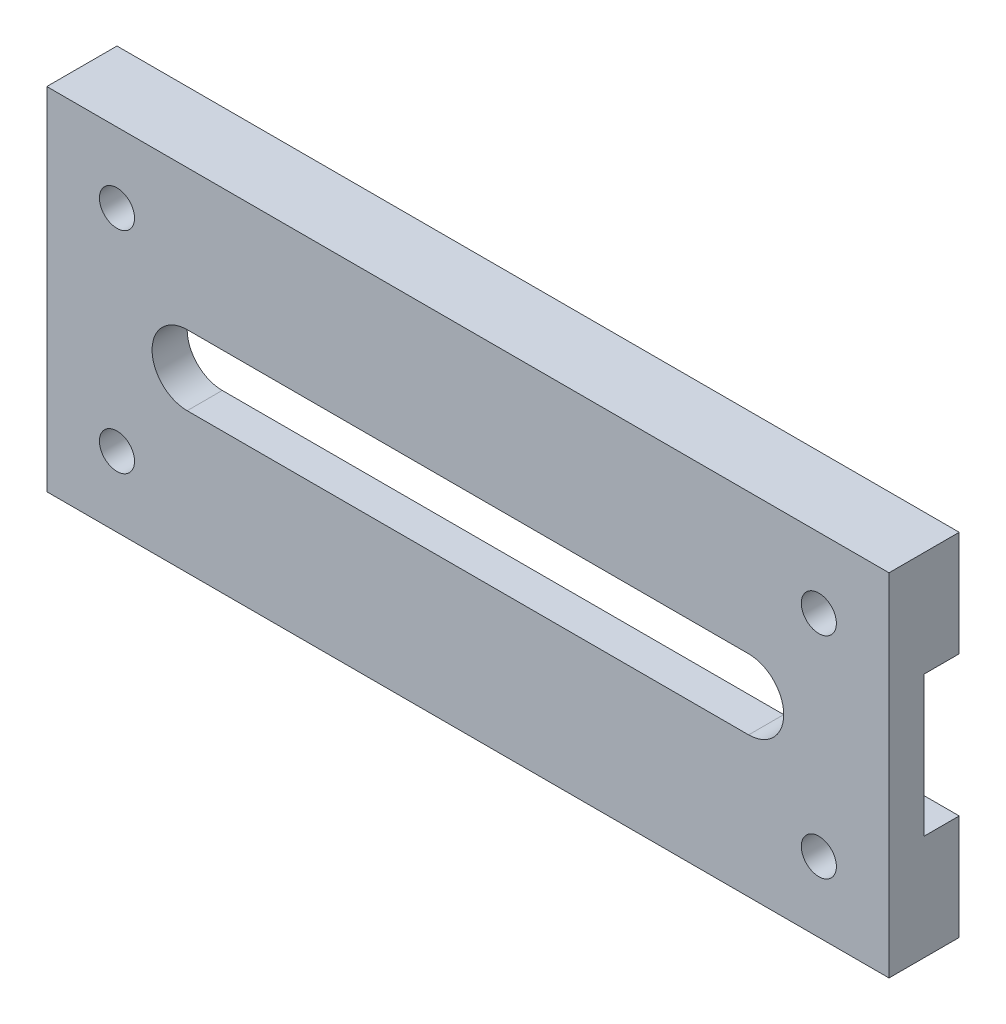
SolidWorks part; units mm, degrees
ref_plane "Front Plane" through (0, 0, 0) normal (0, 0, 1) x (1, 0, 0)
ref_plane "Top Plane" through (0, 0, 0) normal (0, 1, 0) x (1, 0, 0)
ref_plane "Right Plane" through (0, 0, 0) normal (1, 0, 0) x (0, 0, -1)
sketch "Sketch1" plane through (0, 0, 0) normal (0, 0, 1) x (1, 0, 0)
  line L0 (-50.8, 0) -> (50.8, 0) construction
  line L1 (-76.2, 31.75) -> (76.2, 31.75)
  line L2 (-76.2, 31.75) -> (-76.2, -31.75)
  line L3 (-76.2, -31.75) -> (76.2, -31.75)
  line L4 (76.2, 31.75) -> (76.2, -31.75)
  line L5 (-76.2, 31.75) -> (76.2, -31.75) construction
  line L6 (-76.2, -31.75) -> (76.2, 31.75) construction
  line L7 (-50.8, 6.35) -> (50.8, 6.35)
  line L8 (-50.8, -6.35) -> (50.8, -6.35)
  line L9 (0, 31.75) -> (0, -31.75) construction
  line L10 (-76.2, 0) -> (76.2, 0) construction
  arc A0 (-50.8, 6.35) -> (-50.8, -6.35) centre (-50.8, 0) ccw
  arc A1 (50.8, -6.35) -> (50.8, 6.35) centre (50.8, 0) ccw
  circle A2 centre (-63.5, 19.05) radius 3.175
  circle A3 centre (63.5, 19.05) radius 3.175
  circle A4 centre (63.5, -19.05) radius 3.175
  circle A5 centre (-63.5, -19.05) radius 3.175
  point P0 (0, 0)
  point P8 (0, 0)
  dimension "D2" = 6.35
  dimension "D5" = 6.35
  dimension "D1" = 101.6
  dimension "D3" = 63.5
  dimension "D4" = 152.4
  dimension "D6" = 12.7
  dimension "D7" = 12.7
extrude "Boss-Extrude1" add sketch "Sketch1" along normal blind 12.7
sketch "Sketch2" plane through (-76.2, 0, 0) normal (-1, 0, 0) x (0, 0, 1)
  line L1 (-6.35, 12.7) -> (6.35, 12.7)
  line L2 (-6.35, 12.7) -> (-6.35, -12.7)
  line L3 (-6.35, -12.7) -> (6.35, -12.7)
  line L4 (6.35, 12.7) -> (6.35, -12.7)
  line L5 (-6.35, 12.7) -> (6.35, -12.7) construction
  line L6 (-6.35, -12.7) -> (6.35, 12.7) construction
  point P0 (0, 0)
  dimension "D1" = 25.4
  dimension "D2" = 12.7
extrude "Cut-Extrude1" cut sketch "Sketch2" against normal through all
